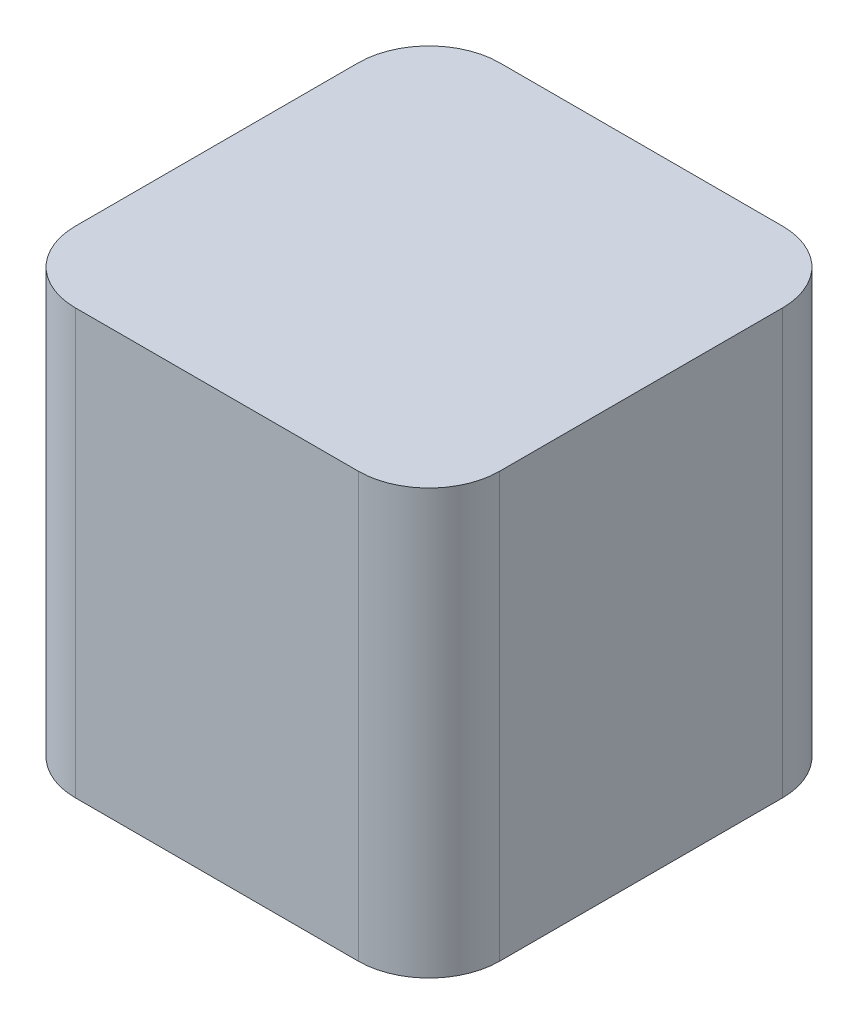
SolidWorks part; units mm, degrees
ref_plane "Front Plane" through (0, 0, 0) normal (0, 0, 1) x (1, 0, 0)
ref_plane "Top Plane" through (0, 0, 0) normal (0, 1, 0) x (1, 0, 0)
ref_plane "Right Plane" through (0, 0, 0) normal (1, 0, 0) x (0, 0, -1)
sketch "Sketch1" plane through (0, 0, 0) normal (0, 1, 0) x (1, 0, 0)
  line L1 (-15, 15) -> (15, 15)
  line L2 (-15, 15) -> (-15, -15)
  line L3 (-15, -15) -> (15, -15)
  line L4 (15, 15) -> (15, -15)
  line L5 (-15, 15) -> (15, -15) construction
  line L6 (-15, -15) -> (15, 15) construction
  point P0 (0, 0)
  dimension "D1" = 30
  dimension "D2" = 30
extrude "Boss-Extrude1" add sketch "Sketch1" along normal blind 30
fillet "Fillet1" radius 5 1 edges at (15, 15, 15)
fillet "Fillet2" radius 5 1 edges at (15, 15, -15)
fillet "Fillet3" radius 5 1 edges at (-15, 15, 15)
fillet "Fillet4" radius 5 1 edges at (-15, 15, -15)
